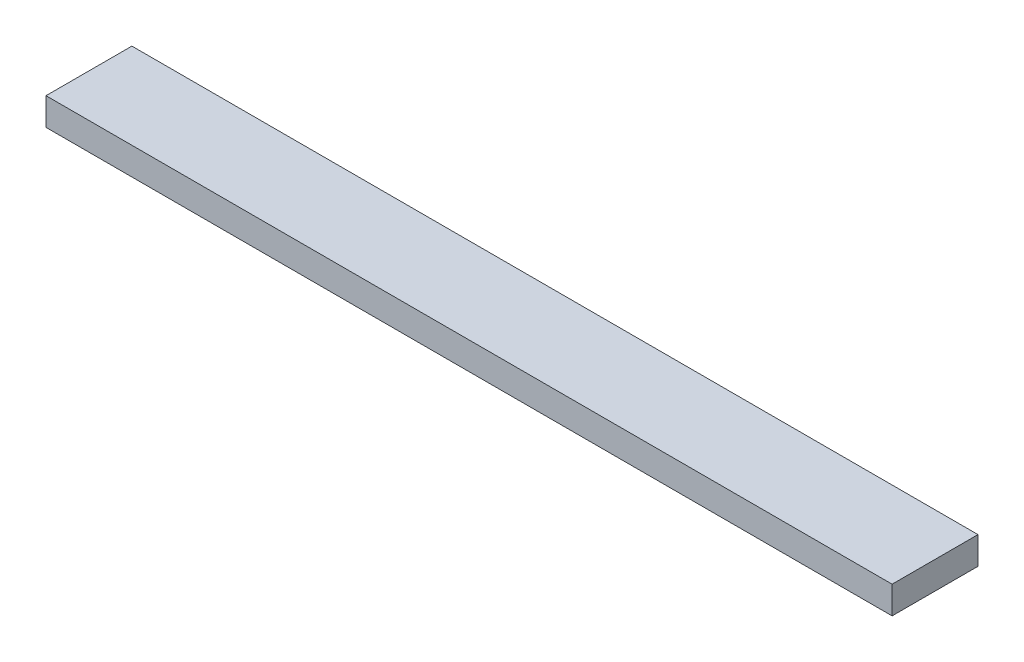
SolidWorks part; units mm, degrees
ref_plane "Front Plane" through (0, 0, 0) normal (0, 0, 1) x (1, 0, 0)
ref_plane "Top Plane" through (0, 0, 0) normal (0, 1, 0) x (1, 0, 0)
ref_plane "Right Plane" through (0, 0, 0) normal (1, 0, 0) x (0, 0, -1)
sketch "Sketch1" plane through (0, 0, 0) normal (0, 1, 0) x (1, 0, 0)
  line L1 (-43.9163, 11.5679) -> (54.5837, 11.5679)
  line L2 (-43.9163, 11.5679) -> (-43.9163, 1.5679)
  line L3 (-43.9163, 1.5679) -> (54.5837, 1.5679)
  line L4 (54.5837, 11.5679) -> (54.5837, 1.5679)
  dimension "D1" = 98.5
  dimension "D2" = 10
extrude "Boss-Extrude1" add sketch "Sketch1" along normal blind 3.2
equation "\"phone support length\"= 98.5"
equation "\"phone support width\"= 10"
equation "\"D1@Sketch1\"=\"phone support length\""
equation "\"D2@Sketch1\"=\"phone support width\""
equation "\"Thinner acrylic\"= 3.2"
equation "\"D1@Boss-Extrude1\"=\"Thinner acrylic\""
